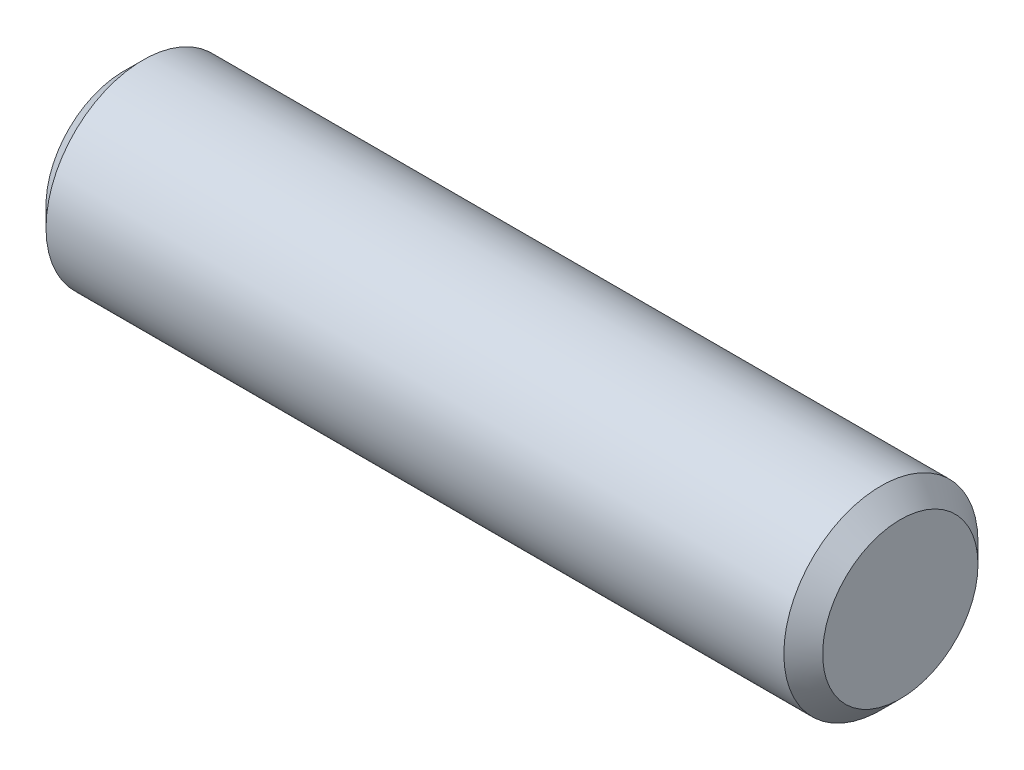
SolidWorks part; units mm, degrees
ref_plane "Front" through (0, 0, 0) normal (0, 0, 1) x (1, 0, 0)
ref_plane "Top" through (0, 0, 0) normal (0, 1, 0) x (1, 0, 0)
ref_plane "Right" through (0, 0, 0) normal (1, 0, 0) x (0, 0, -1)
sketch "Sketch1" plane through (0, 0, 0) normal (0, 0, 1) x (1, 0, 0)
  line L0 (-9.525, 0) -> (9.525, 0) construction
  line L1 (9.525, 2.3813) -> (9.525, -2.3813) construction
  line L2 (-9.525, 2.3813) -> (-9.525, -2.3813) construction
  dimension "Length" = 19.05
  dimension "Diameter" = 4.7625
sketch "Sketch2" plane through (0, 0, 0) normal (1, 0, 0) x (0, 0, -1)
  circle A0 centre (0, 0) radius 2.3813
extrude "Extrude1" add sketch "Sketch2" against normal up to vertex (9.525 mm away) and the other way up to vertex (9.525 mm away) up to point (-9.525, 2.3813, 0) other way up to point (9.525, 2.3813, 0)
chamfer "Chamfer1" distance 0.4763 angle 45 2 edges at (9.525, 0, -2.3813) (-9.525, 0, -2.3813)
equation "\"D1@Chamfer1\" = \"Diameter@Sketch1\"*.1"
